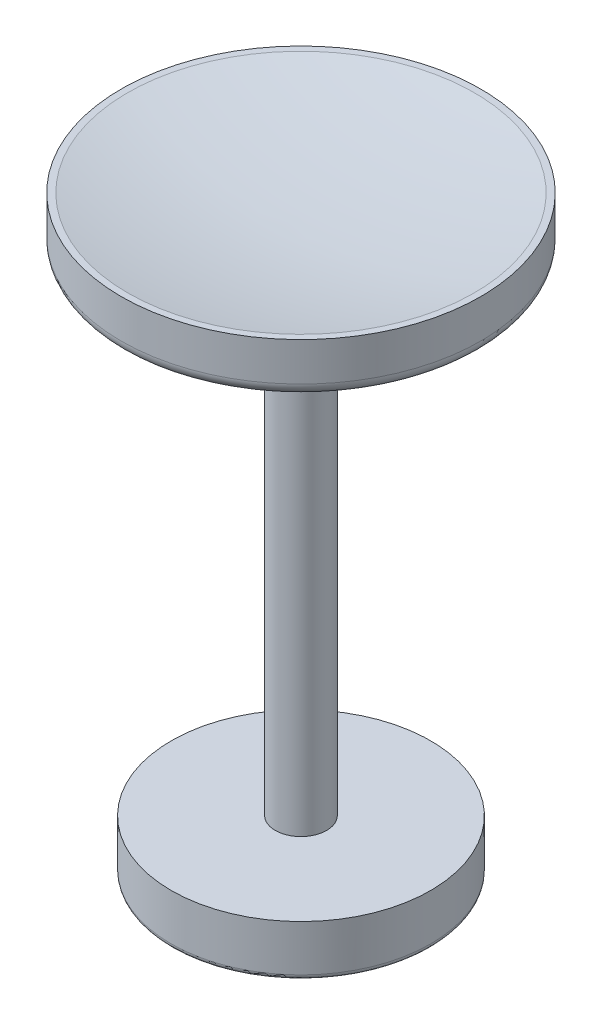
SolidWorks part; units mm, degrees
ref_plane "Front Plane" through (0, 0, 0) normal (0, 0, 1) x (1, 0, 0)
ref_plane "Top Plane" through (0, 0, 0) normal (0, 1, 0) x (1, 0, 0)
ref_plane "Right Plane" through (0, 0, 0) normal (1, 0, 0) x (0, 0, -1)
sketch "Sketch1" plane through (0, 0, 0) normal (0, 1, 0) x (1, 0, 0)
  circle A0 centre (0, 0) radius 17.78
  dimension "D1" = 35.56
extrude "Boss-Extrude1" add sketch "Sketch1" along normal blind 2.54
sketch "Sketch2" plane through (0, 0, 0) normal (1, 0, 0) x (0, 0, -1)
  line L0 (-17.78, 2.54) -> (-17.78, 5.08)
  line L1 (-17.78, 5.08) -> (-17.145, 5.08)
  line L2 (0, 3.175) -> (15.8716, 3.175) construction
  line L3 (17.78, 2.54) -> (-17.78, 2.54) construction
  line L4 (0, 3.175) -> (0, 2.54)
  line L5 (0, 2.54) -> (-17.78, 2.54)
  line L6 (0, 0) -> (0, -53.34)
  line L7 (0, -53.34) -> (-12.827, -53.34)
  line L8 (-12.827, -53.34) -> (-12.827, -48.26)
  line L9 (-12.827, -48.26) -> (-2.54, -48.26)
  line L10 (-2.54, -48.26) -> (-2.54, 0)
  line L11 (-17.78, 0) -> (17.78, 0) construction
  line L12 (-2.54, 0) -> (0, 0)
  arc A0 (-17.145, 5.08) -> (0, 3.175) centre (0, 81.28) ccw
  dimension "D1" = 2.54
  dimension "D2" = 0.635
  dimension "D3" = 0.635
  dimension "D4" = 2.54
  dimension "D5" = 5.08
  dimension "D6" = 53.34
  dimension "D7" = 12.827
revolve "Revolve1" add sketch "Sketch2" angle 360 about L6
fillet "Fillet1" radius 0.508 1 edges at (0, -53.34, 12.827)
fillet "Fillet2" radius 1.27 1 edges at (0, 0, 17.78)
